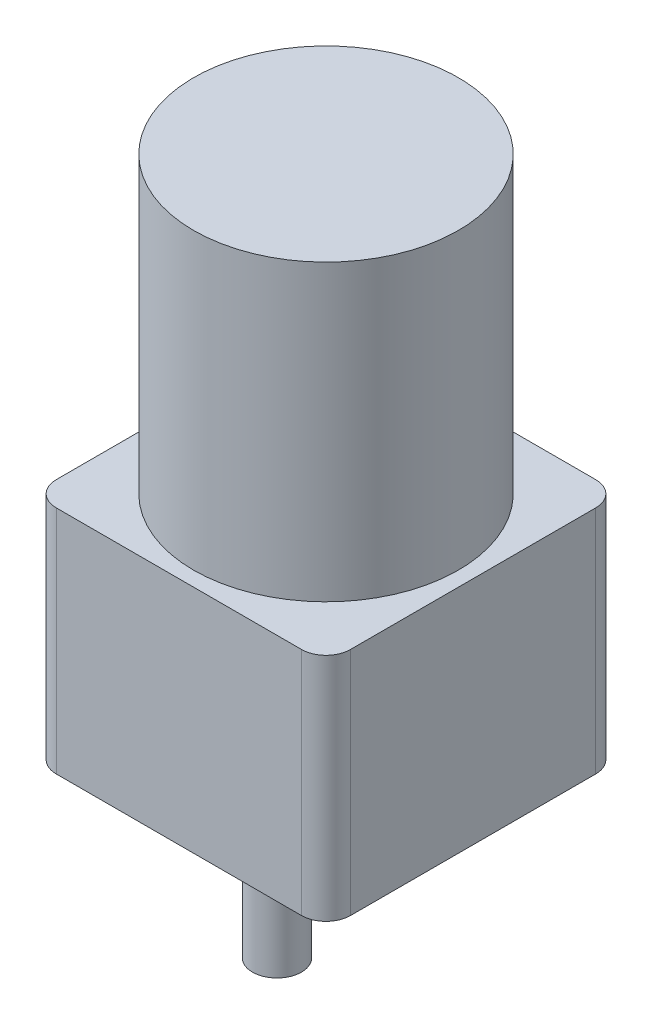
SolidWorks part; units mm, degrees
ref_plane "Front Plane" through (0, 0, 0) normal (0, 0, 1) x (1, 0, 0)
ref_plane "Top Plane" through (0, 0, 0) normal (0, 1, 0) x (1, 0, 0)
ref_plane "Right Plane" through (0, 0, 0) normal (1, 0, 0) x (0, 0, -1)
sketch "Sketch1" plane through (0, 0, 0) normal (0, 1, 0) x (1, 0, 0)
  line L1 (-30, 30) -> (30, 30)
  line L2 (-30, 30) -> (-30, -30)
  line L3 (-30, -30) -> (30, -30)
  line L4 (30, 30) -> (30, -30)
  line L5 (-30, 30) -> (30, -30) construction
  line L6 (-30, -30) -> (30, 30) construction
  point P0 (0, 0)
extrude "Boss-Extrude1" add sketch "Sketch1" along normal blind 47
fillet "Fillet1" radius 5 4 edges at (-30, 23.5, -30) (30, 23.5, -30) (30, 23.5, 30) (-30, 23.5, 30)
sketch "Sketch2" plane through (0, 47, 0) normal (0, 1, 0) x (1, 0, 0)
  circle A0 centre (0, 0) radius 27
extrude "Boss-Extrude2" add sketch "Sketch2" along normal blind 60
sketch "Sketch3" plane through (0, 0, 0) normal (0, -1, 0) x (1, 0, 0)
  line L0 (-25, 30) -> (25, 30) construction
  line L1 (-30, -25) -> (-30, 25) construction
  circle A0 centre (0, 10) radius 5
  dimension "D1" = 20
  dimension "D2" = 30
extrude "Boss-Extrude3" add sketch "Sketch3" along normal blind 30
